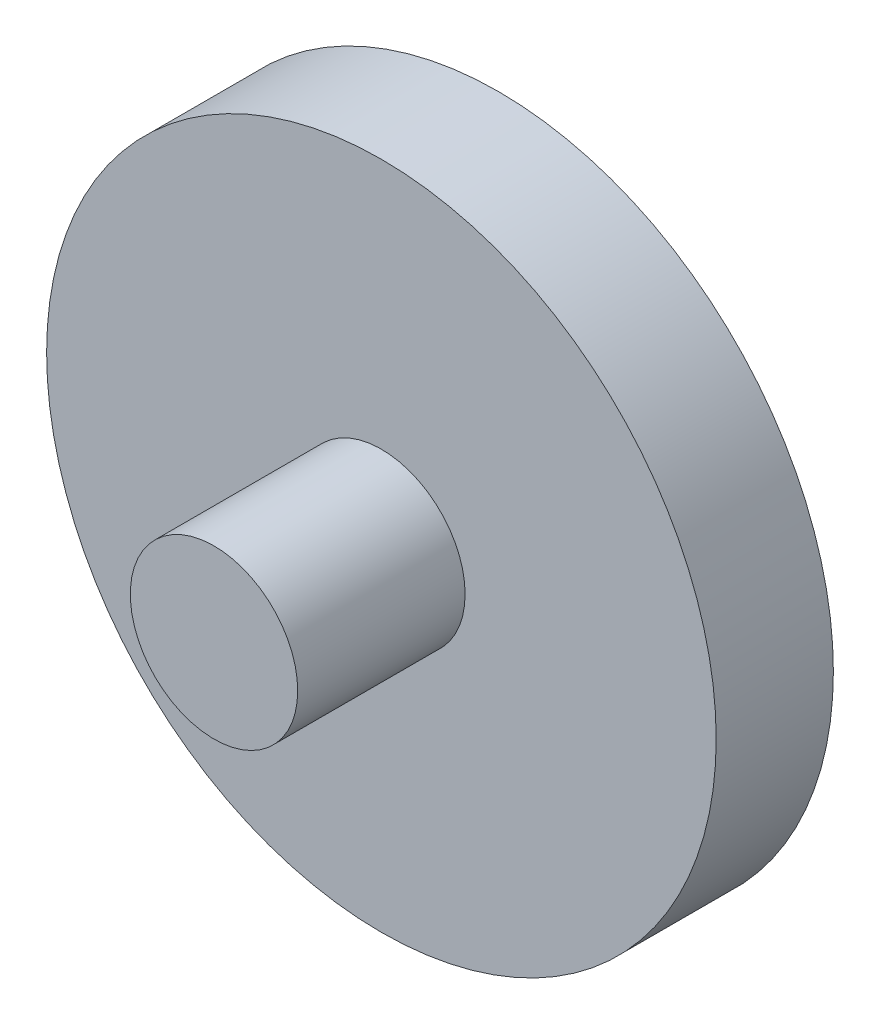
SolidWorks part; units mm, degrees
ref_plane "Plan de face" through (0, 0, 0) normal (0, 0, 1) x (1, 0, 0)
ref_plane "Plan de dessus" through (0, 0, 0) normal (0, 1, 0) x (1, 0, 0)
ref_plane "Plan de droite" through (0, 0, 0) normal (1, 0, 0) x (0, 0, -1)
sketch "Esquisse1" plane through (0, 0, 0) normal (0, 0, 1) x (1, 0, 0)
  circle A0 centre (0, 0) radius 20
  dimension "D1" = 40
extrude "Boss.-Extru.1" add sketch "Esquisse1" along normal blind 7
sketch "Esquisse2" plane through (0, 0, 7) normal (0, 0, 1) x (1, 0, 0)
  circle A0 centre (0, 0) radius 5
  dimension "D1" = 10
extrude "Boss.-Extru.2" add sketch "Esquisse2" along normal blind 10
